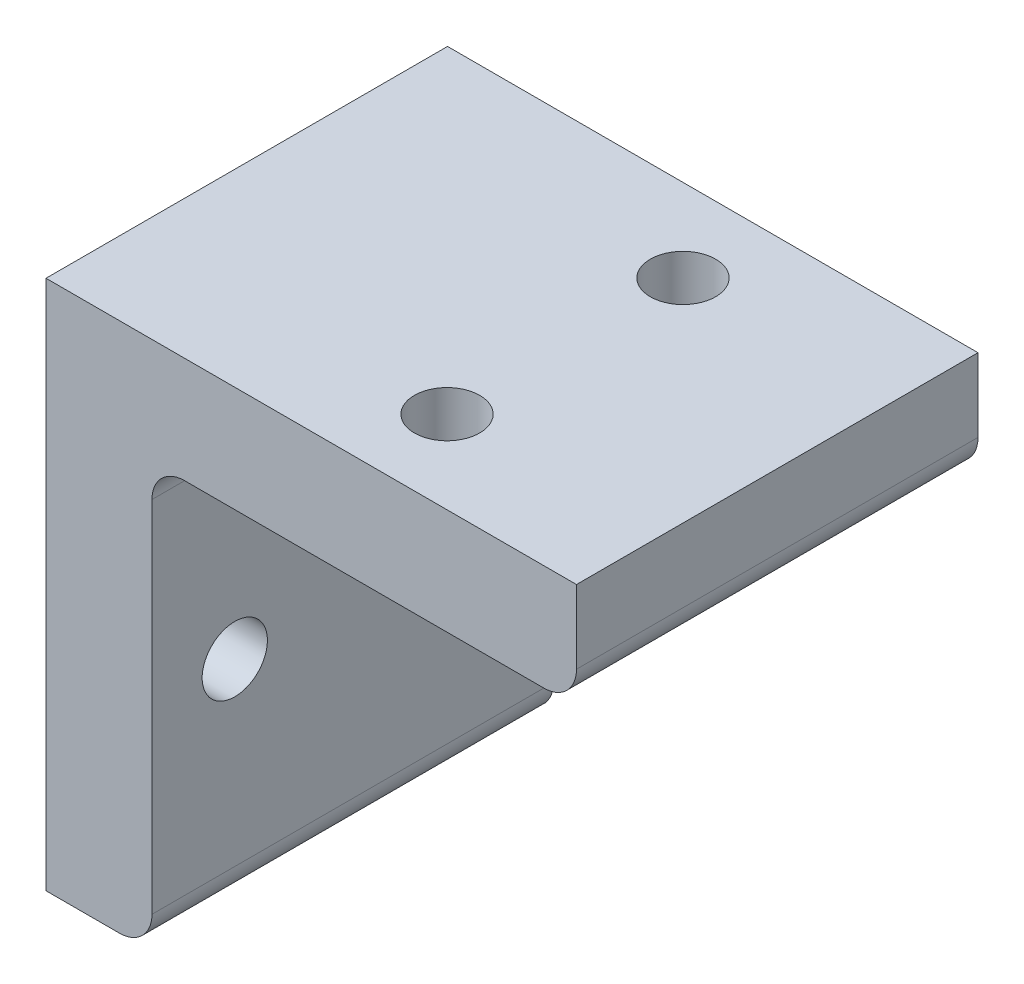
SolidWorks part; units mm, degrees
ref_plane "Front Plane" through (0, 0, 0) normal (0, 0, 1) x (1, 0, 0)
ref_plane "Top Plane" through (0, 0, 0) normal (0, 1, 0) x (1, 0, 0)
ref_plane "Right Plane" through (0, 0, 0) normal (1, 0, 0) x (0, 0, -1)
sketch "Sketch1" plane through (0, 0, 0) normal (1, 0, 0) x (0, 0, -1)
  line L1 (-17.0307, -22.5) -> (17.0307, -22.5)
  line L2 (-17.0307, -22.5) -> (-17.0307, 22.5)
  line L3 (-17.0307, 22.5) -> (17.0307, 22.5)
  line L4 (17.0307, -22.5) -> (17.0307, 22.5)
  line L5 (-17.0307, -22.5) -> (17.0307, 22.5) construction
  line L6 (-17.0307, 22.5) -> (17.0307, -22.5) construction
  point P0 (0, 0)
  dimension "D1" = 34.0614
  dimension "D2" = 45
extrude "Boss-Extrude1" add sketch "Sketch1" along normal blind 8.9916
sketch "Sketch2" plane through (8.9916, 0, 0) normal (1, 0, 0) x (0, 0, -1)
  line L0 (17.0307, -22.5) -> (17.0307, 22.5) construction
  line L1 (-17.0307, 22.5) -> (17.0307, 22.5)
  line L2 (-17.0307, 22.5) -> (-17.0307, 13.5084)
  line L3 (-17.0307, 13.5084) -> (17.0307, 13.5084)
  line L4 (17.0307, 22.5) -> (17.0307, 13.5084)
  dimension "D1" = 8.9916
extrude "Boss-Extrude2" add sketch "Sketch2" along normal blind 36.0084
sketch "Sketch3" plane through (45, 0, 0) normal (1, 0, 0) x (0, 0, -1)
  line L0 (0, 22.5) -> (0, 13.5084) construction
  line L1 (17.0307, 22.5) -> (-17.0307, 22.5) construction
  line L2 (-17.0307, 13.5084) -> (17.0307, 13.5084) construction
  line L4 (0, 22.5) -> (17.0307, 22.5)
  line L5 (0, 22.5) -> (0, 13.5084)
  line L6 (0, 13.5084) -> (17.0307, 13.5084)
  line L7 (17.0307, 22.5) -> (17.0307, 13.5084)
sketch "Sketch5" plane through (8.9916, 0, 0) normal (1, 0, 0) x (0, 0, -1)
  line L0 (-10.0076, -22.5) -> (-10.0076, 13.5084) construction
  line L3 (-17.0307, -4.4958) -> (17.0307, -4.4958) construction
  line L4 (-17.0307, 13.5084) -> (-17.0307, -22.5) construction
  line L5 (17.0307, -22.5) -> (17.0307, 13.5084) construction
  line L6 (-17.0307, -22.5) -> (17.0307, -22.5) construction
  line L7 (-17.0307, 13.5084) -> (17.0307, 13.5084) construction
  line L8 (10.0076, -22.5) -> (10.0076, 13.5084) construction
  circle A0 centre (-10.0076, -4.4958) radius 2.7686
  circle A1 centre (10.0076, -4.4958) radius 2.6416
  dimension "D3" = 5.5372
  dimension "D4" = 5.2832
  dimension "D1" = 7.0231
  dimension "D2" = 7.0231
extrude "Cut-Extrude2" cut sketch "Sketch5" against normal up to next
sketch "Sketch6" plane through (0, 22.5, 0) normal (0, 1, 0) x (1, 0, 0)
  line L0 (26.9957, 17.0307) -> (26.9957, -17.0307) construction
  line L1 (45, 17.0307) -> (0, 17.0307) construction
  line L2 (45, -17.0307) -> (0, -17.0307) construction
  line L3 (45, 0) -> (45, 17.0307) construction
  line L4 (0, 10.0076) -> (45, 10.0076) construction
  line L5 (0, 17.0307) -> (0, -17.0307) construction
  line L6 (0, -10.0076) -> (45, -10.0076) construction
  line L7 (45, 17.0307) -> (45, -17.0307) construction
  circle A0 centre (26.9957, 10.0076) radius 2.7686
  circle A1 centre (26.9957, -10.0076) radius 2.7686
  point P16 (26.9957, 10.0076)
  point P17 (26.9957, -10.0076)
  dimension "D4" = 5.5372
  dimension "D5" = 5.5372
  dimension "D1" = 18.0043
  dimension "D2" = 7.0231
  dimension "D3" = 7.0231
extrude "Cut-Extrude3" cut sketch "Sketch6" against normal up to next
fillet "Fillet1" radius 2.7686 3 edges at (8.9916, -22.5, 0) (45, 13.5084, 0)
